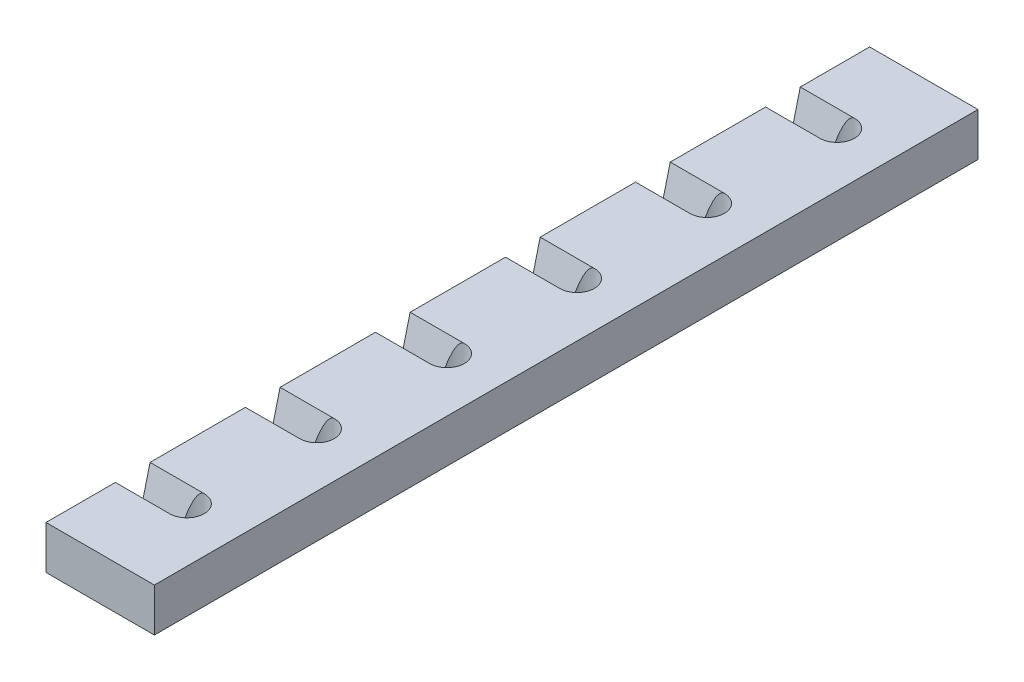
SolidWorks part; units mm, degrees
ref_plane "Front Plane" through (0, 0, 0) normal (0, 0, 1) x (1, 0, 0)
ref_plane "Top Plane" through (0, 0, 0) normal (0, 1, 0) x (1, 0, 0)
ref_plane "Right Plane" through (0, 0, 0) normal (1, 0, 0) x (0, 0, -1)
sketch "Sketch1" plane through (0, 0, 0) normal (0, 0, 1) x (1, 0, 0)
  line L1 (-25, -10) -> (25, -10)
  line L2 (-25, -10) -> (-25, 10)
  line L3 (-25, 10) -> (25, 10)
  line L4 (25, -10) -> (25, 10)
  line L5 (-25, -10) -> (25, 10) construction
  line L6 (-25, 10) -> (25, -10) construction
  point P0 (0, 0)
  dimension "D1" = 50
  dimension "D2" = 20
extrude "Boss-Extrude1" add sketch "Sketch1" against normal blind 380
sketch "Sketch2" plane through (0, 10, 0) normal (0, 1, 0) x (1, 0, 0)
  line L0 (25, 0) -> (-25, 0) construction
  circle A0 centre (0, 40) radius 8
  circle A1 centre (0, 100) radius 8
  circle A2 centre (0, 160) radius 8
  circle A3 centre (0, 220) radius 8
  circle A4 centre (0, 280) radius 8
  circle A5 centre (0, 340) radius 8
  dimension "D7" = 16
  dimension "D8" = 16
  dimension "D9" = 16
  dimension "D10" = 16
  dimension "D11" = 16
  dimension "D12" = 16
  dimension "D1" = 40
  dimension "D2" = 60
  dimension "D3" = 60
  dimension "D4" = 60
  dimension "D5" = 60
  dimension "D6" = 60
extrude "Cut-Extrude1" cut sketch "Sketch2" against normal through all
sketch "Sketch3" plane through (-25, 0, 0) normal (-1, 0, 0) x (0, 0, 1)
  line L0 (-348, 10) -> (-343, -10)
  line L1 (-380, 10) -> (0, 10) construction
  line L2 (-380, -10) -> (0, -10) construction
  line L3 (-343, -10) -> (-337, -10)
  line L4 (-337, -10) -> (-332, 10)
  line L5 (-332, 10) -> (-348, 10)
  line L6 (-288, 10) -> (-283, -10)
  line L7 (-277, -10) -> (-272, 10)
  line L8 (-283, -10) -> (-277, -10)
  line L9 (-272, 10) -> (-288, 10)
  line L10 (-228, 10) -> (-223, -10)
  line L11 (-217, -10) -> (-212, 10)
  line L12 (-223, -10) -> (-217, -10)
  line L13 (-212, 10) -> (-228, 10)
  line L14 (-168, 10) -> (-163, -10)
  line L15 (-157, -10) -> (-152, 10)
  line L16 (-163, -10) -> (-157, -10)
  line L17 (-152, 10) -> (-168, 10)
  line L18 (-108, 10) -> (-103, -10)
  line L19 (-97, -10) -> (-92, 10)
  line L20 (-103, -10) -> (-97, -10)
  line L21 (-92, 10) -> (-108, 10)
  line L22 (-48, 10) -> (-43, -10)
  line L23 (-37, -10) -> (-32, 10)
  line L24 (-43, -10) -> (-37, -10)
  line L25 (-32, 10) -> (-48, 10)
  dimension "D1" = 32
  dimension "D2" = 16
  dimension "D3" = 6
  dimension "D4" = 37
  dimension "D6" = 44
  dimension "D7" = 54
  dimension "D5" = 6
extrude "Cut-Extrude2" cut sketch "Sketch3" against normal up to next
